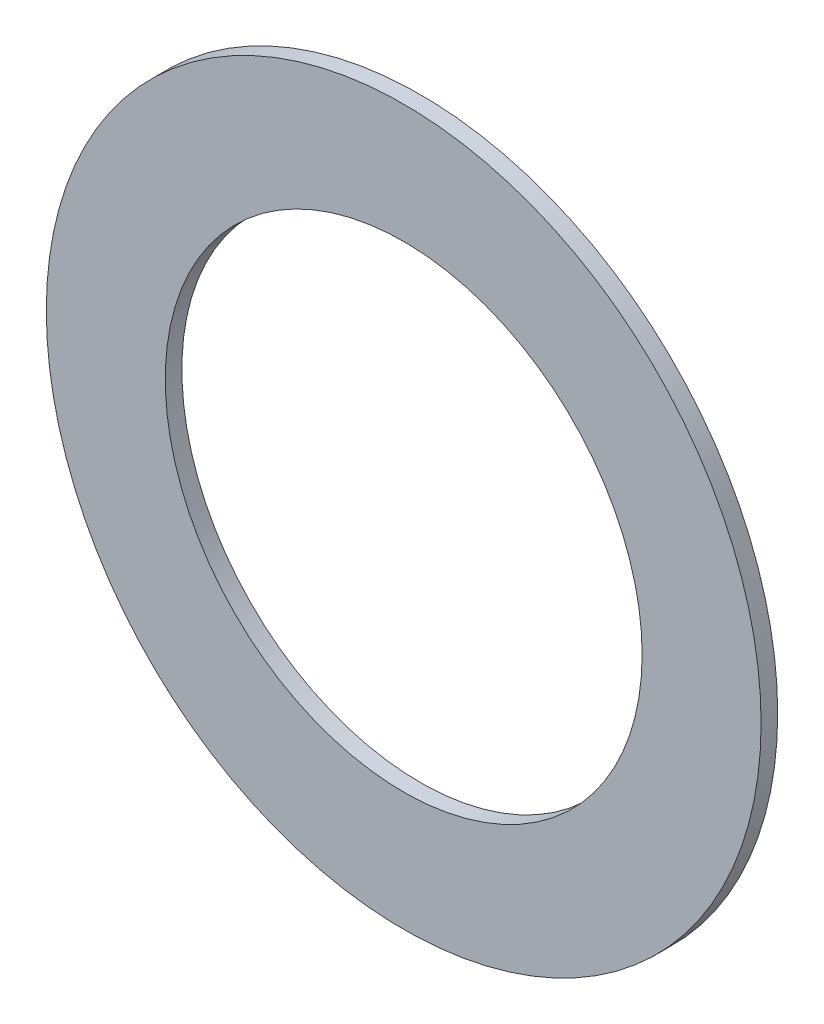
SolidWorks part; units mm, degrees
material "Plain Carbon Steel"
ref_plane "Front Plane" through (0, 0, 0) normal (0, 0, 1) x (1, 0, 0)
ref_plane "Top Plane" through (0, 0, 0) normal (0, 1, 0) x (1, 0, 0)
ref_plane "Right Plane" through (0, 0, 0) normal (1, 0, 0) x (0, 0, -1)
sketch "Sketch1" plane through (0, 0, 0) normal (0, 0, 1) x (1, 0, 0)
  circle A0 centre (164.7998, 1350.514) radius 22.8092 construction
  circle A1 centre (164.7998, 1350.514) radius 22.8092
  circle A4 centre (164.7998, 1350.514) radius 34.1884
  circle A5 centre (164.7998, 1350.514) radius 34.1884
  dimension "D1" = 1.27
extrude "Boss-Extrude1" add sketch "Sketch1" along normal blind 1.5875
